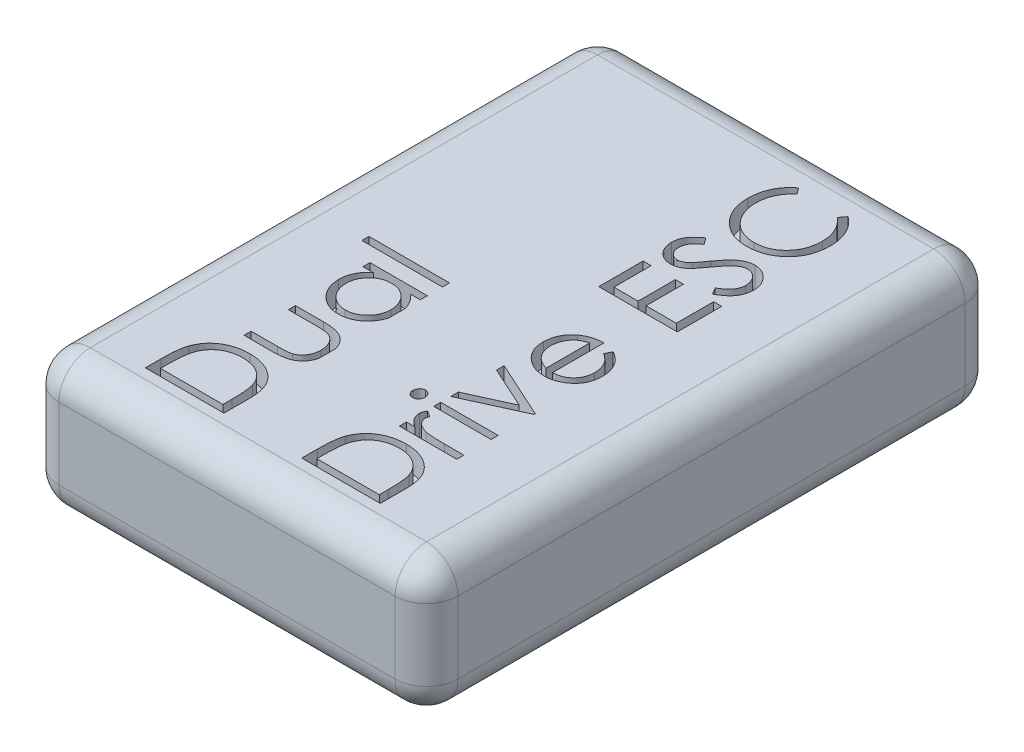
SolidWorks part; units mm, degrees
ref_plane "Front Plane" through (0, 0, 0) normal (0, 0, 1) x (1, 0, 0)
ref_plane "Top Plane" through (0, 0, 0) normal (0, 1, 0) x (1, 0, 0)
ref_plane "Right Plane" through (0, 0, 0) normal (1, 0, 0) x (0, 0, -1)
sketch "Sketch1" plane through (0, 0, 0) normal (0, 1, 0) x (1, 0, 0)
  line L1 (0, 0) -> (17.78, 0)
  line L2 (0, 0) -> (0, 25.4)
  line L3 (0, 25.4) -> (17.78, 25.4)
  line L4 (17.78, 0) -> (17.78, 25.4)
  dimension "D1" = 17.78
  dimension "D2" = 25.4
extrude "Boss-Extrude1" add sketch "Sketch1" along normal blind 6
fillet "Fillet1" radius 1.4 12 edges at (0, 0, -12.7) (8.89, 0, 0) (17.78, 0, -12.7) (8.89, 0, -25.4) (0, 6, -12.7) (17.78, 6, -12.7) (8.89, 6, -25.4) (0, 3, -25.4) (17.78, 3, -25.4) (17.78, 3, 0) (0, 3, 0) (8.89, 6, 0)
sketch "Sketch2" plane through (0, 6, 0) normal (0, 1, 0) x (1, 0, 0)
  line L0 (6.9039, 1.4) -> (6.9039, 24)
  line L1 (1.4, 1.4) -> (16.38, 1.4) construction
  line L2 (16.38, 24) -> (1.4, 24) construction
  line L3 (6.9039, 1.8487) -> (3.4039, 1.8487)
  line L4 (3.4039, 1.8487) -> (3.4039, 2.5554)
  line L5 (6.9039, 2.9334) -> (6.9039, 1.8487)
  line L6 (6.5449, 2.1628) -> (6.5449, 2.5646)
  line L7 (3.7629, 2.4089) -> (3.7629, 2.1628)
  line L8 (3.7629, 2.1628) -> (6.5449, 2.1628)
  line L9 (4.3462, 5.3038) -> (4.3462, 5.6179)
  line L10 (4.3462, 5.6179) -> (5.5325, 5.6179)
  line L11 (5.5325, 7.2782) -> (4.3462, 7.2782)
  line L12 (4.3462, 7.2782) -> (4.3462, 7.5923)
  line L13 (4.3462, 7.5923) -> (5.5914, 7.5923)
  line L14 (5.5683, 5.3038) -> (4.3462, 5.3038)
  line L15 (4.3462, 10.9128) -> (6.9039, 10.9128)
  line L16 (6.9039, 10.9128) -> (6.9039, 10.5987)
  line L17 (6.9039, 10.5987) -> (6.4615, 10.5987)
  line L18 (4.8195, 10.5987) -> (4.3462, 10.5987)
  line L19 (4.3462, 10.5987) -> (4.3462, 10.9128)
  line L20 (3.3141, 11.5859) -> (3.3141, 11.9)
  line L21 (3.3141, 11.9) -> (6.9039, 11.9)
  line L22 (6.9039, 11.9) -> (6.9039, 11.5859)
  line L23 (6.9039, 11.5859) -> (3.3141, 11.5859)
  line L24 (13.8718, 1.8487) -> (10.3718, 1.8487)
  line L25 (10.3718, 1.8487) -> (10.3718, 2.5554)
  line L26 (13.8718, 2.9334) -> (13.8718, 1.8487)
  line L27 (13.5129, 2.1628) -> (13.5129, 2.5646)
  line L28 (10.7308, 2.4089) -> (10.7308, 2.1628)
  line L29 (10.7308, 2.1628) -> (13.5129, 2.1628)
  line L30 (11.3141, 5.259) -> (11.3141, 5.5731)
  line L31 (11.3141, 5.5731) -> (11.6907, 5.5731)
  line L32 (11.3569, 6.4705) -> (11.629, 6.298)
  line L33 (13.0123, 5.5731) -> (13.8718, 5.5731)
  line L34 (13.8718, 5.5731) -> (13.8718, 5.259)
  line L35 (13.8718, 5.259) -> (11.3141, 5.259)
  line L36 (11.3141, 6.7846) -> (11.3141, 7.0987)
  line L37 (11.3141, 7.0987) -> (13.8718, 7.0987)
  line L38 (13.8718, 7.0987) -> (13.8718, 6.7846)
  line L39 (13.8718, 6.7846) -> (11.3141, 6.7846)
  line L40 (11.3141, 7.5474) -> (11.3141, 7.8875)
  line L41 (11.3141, 7.8875) -> (13.1763, 8.7365)
  line L42 (13.1763, 8.7365) -> (11.3141, 9.5856)
  line L43 (11.3141, 9.5856) -> (11.3141, 9.9256)
  line L44 (11.3141, 9.9256) -> (13.8718, 8.759)
  line L45 (13.8718, 8.759) -> (13.8718, 8.7141)
  line L46 (13.8718, 8.7141) -> (11.3141, 7.5474)
  line L47 (13.0641, 12.6081) -> (13.2107, 12.8872)
  line L48 (12.6603, 13.0218) -> (12.6603, 10.7333)
  line L49 (12.3462, 10.7663) -> (12.3462, 12.7077)
  line L50 (10.3718, 15.0859) -> (10.3718, 17.0603)
  line L51 (10.3718, 17.0603) -> (10.7308, 17.0603)
  line L52 (10.7308, 17.0603) -> (10.7308, 15.4)
  line L53 (10.7308, 15.4) -> (11.8077, 15.4)
  line L54 (11.8077, 15.4) -> (11.8077, 17.0603)
  line L55 (11.8077, 17.0603) -> (12.1667, 17.0603)
  line L56 (12.1667, 17.0603) -> (12.1667, 15.4)
  line L57 (12.1667, 15.4) -> (13.5129, 15.4)
  line L58 (13.5129, 15.4) -> (13.5129, 17.0603)
  line L59 (13.5129, 17.0603) -> (13.8718, 17.0603)
  line L60 (13.8718, 17.0603) -> (13.8718, 15.0859)
  line L61 (13.8718, 15.0859) -> (10.3718, 15.0859)
  line L62 (13.1967, 17.3295) -> (13.0193, 17.6254)
  line L63 (10.8745, 19.3487) -> (11.0898, 19.0648)
  line L64 (11.0141, 23.3423) -> (11.2244, 23.0675)
  line L65 (13.0193, 23.0675) -> (13.2275, 23.3423)
  spline S0 degree 3 poles (3.4039, 2.5554) (3.4044, 2.6742) (3.4069, 2.8459) (3.4202, 3.0661) (3.4342, 3.2115) (3.4514, 3.344) (3.4785, 3.4953) (3.5071, 3.601) (3.5301, 3.666) knots 0 0 0 0 0.317406 0.458844 0.589367 0.707831 0.81577 1 1 1 1
  spline S1 degree 3 poles (3.5301, 3.666) (3.5587, 3.7468) (3.6111, 3.8635) (3.6987, 4.0082) (3.7726, 4.1087) (3.8544, 4.2022) (3.9436, 4.2899) (4.0422, 4.3696) (4.1483, 4.4425) (4.2606, 4.5082) (4.3789, 4.5654) (4.5027, 4.6128) (4.6315, 4.6522) (4.7657, 4.6832) (4.9547, 4.7121) (5.0999, 4.721) (5.1981, 4.7205) knots 0 0 0 0 0.121697 0.181159 0.240077 0.298686 0.357633 0.417592 0.478482 0.540397 0.602336 0.664997 0.728553 0.793646 0.860531 1 1 1 1
  spline S2 degree 3 poles (5.1981, 4.7205) (5.2833, 4.7209) (5.4093, 4.7133) (5.5741, 4.6913) (5.6917, 4.6663) (5.8061, 4.6359) (5.9159, 4.5969) (6.0222, 4.5523) (6.1237, 4.5003) (6.2197, 4.4431) (6.3103, 4.3821) (6.3934, 4.3159) (6.4713, 4.2464) (6.5419, 4.1721) (6.6063, 4.0938) (6.6637, 4.0112) (6.7147, 3.9238) (6.7604, 3.8304) (6.7985, 3.7281) (6.8315, 3.6173) (6.8578, 3.4975) (6.8789, 3.369) (6.8985, 3.1802) (6.9044, 3.0337) (6.9039, 2.9334) knots 0 0 0 0 0.090813 0.134304 0.177036 0.218837 0.260262 0.3011 0.341637 0.381609 0.420148 0.45791 0.494761 0.531219 0.566961 0.602742 0.638232 0.674761 0.713378 0.754425 0.797802 0.843979 0.893064 1 1 1 1
  spline S3 degree 3 poles (6.5449, 2.5646) (6.5449, 2.6756) (6.5427, 2.8353) (6.5332, 3.0389) (6.5236, 3.171) (6.5109, 3.2893) (6.4934, 3.4202) (6.4731, 3.5105) (6.4559, 3.5651) knots 0 0 0 0 0.330628 0.475549 0.606746 0.725024 0.829742 1 1 1 1
  spline S4 degree 3 poles (6.4559, 3.5651) (6.4344, 3.6283) (6.3986, 3.7215) (6.3338, 3.8358) (6.2804, 3.9159) (6.2197, 3.9902) (6.1532, 4.0596) (6.0804, 4.1241) (6.0014, 4.1825) (5.9172, 4.2354) (5.8276, 4.2808) (5.7339, 4.3204) (5.6352, 4.3517) (5.5323, 4.3764) (5.3864, 4.4) (5.2737, 4.4064) (5.1974, 4.4064) knots 0 0 0 0 0.123333 0.183117 0.241773 0.300566 0.359665 0.418864 0.479511 0.540462 0.601913 0.664467 0.727807 0.792475 0.859249 1 1 1 1
  spline S5 degree 3 poles (5.1974, 4.4064) (5.1169, 4.4073) (4.9984, 4.399) (4.8445, 4.3737) (4.7356, 4.3469) (4.6309, 4.3128) (4.5311, 4.2702) (4.4351, 4.2215) (4.3451, 4.1636) (4.26, 4.1002) (4.182, 4.0298) (4.111, 3.9536) (4.0459, 3.8724) (3.9892, 3.7838) (3.9207, 3.6572) (3.8828, 3.5545) (3.861, 3.4844) knots 0 0 0 0 0.137813 0.203226 0.267174 0.330024 0.391794 0.453084 0.514334 0.575 0.634865 0.694116 0.753442 0.813126 0.87408 1 1 1 1
  spline S6 degree 3 poles (3.861, 3.4844) (3.8423, 3.4224) (3.821, 3.321) (3.8003, 3.1762) (3.7861, 3.0483) (3.7761, 2.9073) (3.7655, 2.6928) (3.7625, 2.5251) (3.7629, 2.4089) knots 0 0 0 0 0.179285 0.286583 0.405111 0.535593 0.67819 1 1 1 1
  spline S7 degree 3 poles (5.5325, 5.6179) (5.5991, 5.6183) (5.695, 5.6185) (5.8172, 5.6245) (5.8962, 5.6299) (5.9669, 5.6369) (6.0444, 5.6472) (6.0983, 5.6577) (6.1306, 5.6677) knots 0 0 0 0 0.33212 0.477936 0.609932 0.727032 0.831671 1 1 1 1
  spline S8 degree 3 poles (6.1306, 5.6677) (6.1682, 5.6808) (6.2243, 5.7018) (6.292, 5.7422) (6.3403, 5.775) (6.3851, 5.8129) (6.4263, 5.8554) (6.4655, 5.901) (6.5119, 5.9687) (6.5616, 6.0614) (6.6204, 6.2274) (6.6345, 6.3621) (6.6347, 6.453) knots 0 0 0 0 0.119716 0.178086 0.235971 0.29461 0.353536 0.413161 0.474545 0.599234 0.727029 1 1 1 1
  spline S9 degree 3 poles (6.6347, 6.453) (6.6342, 6.5434) (6.6209, 6.6765) (6.5639, 6.8402) (6.5061, 6.9471) (6.4353, 7.0409) (6.3251, 7.1454) (6.2264, 7.2019) (6.1558, 7.2263) knots 0 0 0 0 0.279837 0.408371 0.533043 0.653596 0.770016 1 1 1 1
  spline S10 degree 3 poles (6.1558, 7.2263) (6.1252, 7.2365) (6.073, 7.2478) (5.9961, 7.2587) (5.9232, 7.2664) (5.8399, 7.2718) (5.7085, 7.2761) (5.605, 7.279) (5.5325, 7.2782) knots 0 0 0 0 0.154074 0.254591 0.371465 0.504755 0.653494 1 1 1 1
  spline S11 degree 3 poles (5.5914, 7.5923) (5.6735, 7.5919) (5.7929, 7.5892) (5.9465, 7.576) (6.0496, 7.5619) (6.1445, 7.5447) (6.2312, 7.5231) (6.3099, 7.4971) (6.3816, 7.4678) (6.4467, 7.4332) (6.5084, 7.3964) (6.5652, 7.3538) (6.6202, 7.3093) (6.6695, 7.2587) (6.717, 7.2059) (6.7597, 7.1478) (6.799, 7.0863) (6.8342, 7.0207) (6.8652, 6.9512) (6.891, 6.8775) (6.912, 6.7997) (6.9288, 6.718) (6.9449, 6.6012) (6.949, 6.5113) (6.9488, 6.4502) knots 0 0 0 0 0.120709 0.175567 0.226556 0.273743 0.317339 0.357879 0.395473 0.431138 0.466151 0.501072 0.535484 0.569994 0.604816 0.639941 0.675791 0.712081 0.749315 0.787578 0.826765 0.867814 0.91015 1 1 1 1
  spline S12 degree 3 poles (6.9488, 6.4502) (6.949, 6.3891) (6.9449, 6.2991) (6.9288, 6.1823) (6.9119, 6.1005) (6.8911, 6.0223) (6.865, 5.9483) (6.8342, 5.8783) (6.7991, 5.8121) (6.7596, 5.7501) (6.7162, 5.6922) (6.6699, 5.6376) (6.6191, 5.5877) (6.5644, 5.5421) (6.5058, 5.5007) (6.4441, 5.4628) (6.378, 5.4284) (6.3055, 5.3989) (6.2252, 5.3729) (6.1363, 5.3516) (6.0388, 5.3342) (5.9333, 5.3203) (5.7756, 5.3068) (5.6529, 5.3043) (5.5683, 5.3038) knots 0 0 0 0 0.088737 0.130549 0.17109 0.210119 0.247908 0.284992 0.321132 0.356538 0.391704 0.426128 0.460451 0.494916 0.529482 0.564528 0.600052 0.637495 0.678178 0.722552 0.770157 0.82186 0.877053 1 1 1 1
  spline S13 degree 3 poles (6.4615, 10.5987) (6.5404, 10.5308) (6.6526, 10.4237) (6.766, 10.2561) (6.8343, 10.1277) (6.8854, 9.9927) (6.9348, 9.8027) (6.9496, 9.6543) (6.9488, 9.554) knots 0 0 0 0 0.26246 0.386305 0.507193 0.627322 0.748159 1 1 1 1
  spline S14 degree 3 poles (6.9488, 9.554) (6.9485, 9.465) (6.9371, 9.3327) (6.8962, 9.1627) (6.8543, 9.0414) (6.7987, 8.9257) (6.7322, 8.8147) (6.653, 8.7088) (6.5624, 8.6097) (6.464, 8.5185) (6.359, 8.4384) (6.248, 8.3717) (6.1323, 8.3159) (6.0109, 8.2729) (5.8402, 8.2322) (5.7075, 8.2207) (5.618, 8.2205) knots 0 0 0 0 0.127433 0.189004 0.24993 0.310668 0.372329 0.434939 0.499576 0.564191 0.626735 0.688109 0.749294 0.810331 0.871901 1 1 1 1
  spline S15 degree 3 poles (5.618, 8.2205) (5.5302, 8.221) (5.3996, 8.2318) (5.2319, 8.2738) (5.1125, 8.3173) (4.9982, 8.3731) (4.8888, 8.441) (4.784, 8.5211) (4.6863, 8.6133) (4.5961, 8.7133) (4.5177, 8.8202) (4.45, 8.9314) (4.3963, 9.0486) (4.3529, 9.1702) (4.3123, 9.3414) (4.3021, 9.4744) (4.3013, 9.5639) knots 0 0 0 0 0.126079 0.186904 0.247574 0.308003 0.369132 0.432033 0.496791 0.561611 0.624914 0.686726 0.748079 0.809582 0.871631 1 1 1 1
  spline S16 degree 3 poles (4.3013, 9.5639) (4.3017, 9.666) (4.3147, 9.8178) (4.3688, 10.0098) (4.4224, 10.1447) (4.4952, 10.2711) (4.6168, 10.4342) (4.7356, 10.5358) (4.8195, 10.5987) knots 0 0 0 0 0.254681 0.376055 0.495308 0.61515 0.738121 1 1 1 1
  spline S17 degree 3 poles (4.6154, 9.5681) (4.6158, 9.4776) (4.6308, 9.3422) (4.6875, 9.1712) (4.7444, 9.0499) (4.8176, 8.9381) (4.9037, 8.8363) (5.0043, 8.7478) (5.1158, 8.6717) (5.2359, 8.6107) (5.403, 8.5528) (5.5341, 8.5335) (5.6215, 8.5346) knots 0 0 0 0 0.169607 0.252496 0.336272 0.419777 0.50203 0.585103 0.669819 0.754165 0.836645 1 1 1 1
  spline S18 degree 3 poles (5.6215, 8.5346) (5.7084, 8.5355) (5.8398, 8.5517) (6.0062, 8.6121) (6.1274, 8.673) (6.2399, 8.75) (6.3424, 8.8384) (6.4298, 8.9406) (6.5031, 9.0535) (6.5622, 9.1741) (6.6176, 9.3436) (6.6351, 9.4764) (6.6347, 9.5653) knots 0 0 0 0 0.162873 0.245092 0.330422 0.416116 0.499851 0.583013 0.66713 0.751291 0.833771 1 1 1 1
  spline S19 degree 3 poles (6.6347, 9.5653) (6.634, 9.6555) (6.6192, 9.7915) (6.5617, 9.9639) (6.5041, 10.0878) (6.4323, 10.2032) (6.3483, 10.3063) (6.2512, 10.3946) (6.1433, 10.4681) (6.0257, 10.5264) (5.8566, 10.5842) (5.7213, 10.5981) (5.6307, 10.5987) knots 0 0 0 0 0.168704 0.252748 0.338456 0.42334 0.505813 0.586129 0.667469 0.748852 0.830411 1 1 1 1
  spline S20 degree 3 poles (5.6307, 10.5987) (5.5611, 10.5985) (5.4581, 10.5897) (5.3259, 10.5585) (5.2325, 10.5261) (5.1438, 10.4836) (5.0594, 10.4324) (4.9795, 10.3715) (4.9054, 10.3019) (4.8377, 10.2257) (4.7774, 10.1452) (4.7278, 10.0592) (4.6867, 9.9693) (4.6541, 9.8752) (4.6244, 9.7416) (4.6144, 9.6382) (4.6154, 9.5681) knots 0 0 0 0 0.129188 0.191219 0.251913 0.312507 0.373494 0.435152 0.498741 0.562095 0.624187 0.685476 0.746097 0.807612 0.869967 1 1 1 1
  spline S21 degree 3 poles (10.3718, 2.5554) (10.3723, 2.6742) (10.3748, 2.8459) (10.3882, 3.0661) (10.4021, 3.2115) (10.4193, 3.344) (10.4464, 3.4953) (10.475, 3.601) (10.498, 3.666) knots 0 0 0 0 0.317406 0.458844 0.589367 0.707831 0.81577 1 1 1 1
  spline S22 degree 3 poles (10.498, 3.666) (10.5266, 3.7468) (10.579, 3.8635) (10.6667, 4.0082) (10.7405, 4.1087) (10.8224, 4.2022) (10.9116, 4.2899) (11.0101, 4.3696) (11.1162, 4.4425) (11.2285, 4.5082) (11.3468, 4.5654) (11.4706, 4.6128) (11.5994, 4.6522) (11.7336, 4.6832) (11.9226, 4.7121) (12.0678, 4.721) (12.166, 4.7205) knots 0 0 0 0 0.121697 0.181159 0.240077 0.298686 0.357633 0.417592 0.478482 0.540397 0.602336 0.664997 0.728553 0.793646 0.860531 1 1 1 1
  spline S23 degree 3 poles (12.166, 4.7205) (12.2513, 4.7209) (12.3773, 4.7133) (12.5421, 4.6913) (12.6597, 4.6663) (12.774, 4.6359) (12.8838, 4.5969) (12.9902, 4.5523) (13.0916, 4.5003) (13.1877, 4.4431) (13.2782, 4.3821) (13.3614, 4.3159) (13.4393, 4.2464) (13.5098, 4.1721) (13.5743, 4.0938) (13.6316, 4.0112) (13.6827, 3.9238) (13.7284, 3.8304) (13.7665, 3.7281) (13.7995, 3.6173) (13.8257, 3.4975) (13.8469, 3.369) (13.8664, 3.1802) (13.8724, 3.0337) (13.8718, 2.9334) knots 0 0 0 0 0.090813 0.134304 0.177036 0.218837 0.260262 0.3011 0.341637 0.381609 0.420148 0.45791 0.494761 0.531219 0.566961 0.602742 0.638232 0.674761 0.713378 0.754425 0.797802 0.843979 0.893064 1 1 1 1
  spline S24 degree 3 poles (13.5129, 2.5646) (13.5128, 2.6756) (13.5107, 2.8353) (13.5011, 3.0389) (13.4915, 3.171) (13.4788, 3.2893) (13.4613, 3.4202) (13.441, 3.5105) (13.4238, 3.5651) knots 0 0 0 0 0.330628 0.475549 0.606746 0.725024 0.829742 1 1 1 1
  spline S25 degree 3 poles (13.4238, 3.5651) (13.4024, 3.6283) (13.3666, 3.7215) (13.3017, 3.8358) (13.2483, 3.9159) (13.1877, 3.9902) (13.1211, 4.0596) (13.0483, 4.1241) (12.9694, 4.1825) (12.8852, 4.2354) (12.7956, 4.2808) (12.7018, 4.3204) (12.6031, 4.3517) (12.5003, 4.3764) (12.3544, 4.4) (12.2417, 4.4064) (12.1653, 4.4064) knots 0 0 0 0 0.123333 0.183117 0.241773 0.300566 0.359665 0.418864 0.479511 0.540462 0.601913 0.664467 0.727807 0.792475 0.859249 1 1 1 1
  spline S26 degree 3 poles (12.1653, 4.4064) (12.0849, 4.4073) (11.9664, 4.399) (11.8125, 4.3737) (11.7035, 4.3469) (11.5988, 4.3128) (11.499, 4.2702) (11.403, 4.2215) (11.313, 4.1636) (11.2279, 4.1002) (11.15, 4.0298) (11.079, 3.9536) (11.0138, 3.8724) (10.9572, 3.7838) (10.8886, 3.6572) (10.8508, 3.5545) (10.829, 3.4844) knots 0 0 0 0 0.137813 0.203226 0.267174 0.330024 0.391794 0.453084 0.514334 0.575 0.634865 0.694116 0.753442 0.813126 0.87408 1 1 1 1
  spline S27 degree 3 poles (10.829, 3.4844) (10.8102, 3.4224) (10.789, 3.321) (10.7682, 3.1762) (10.7541, 3.0483) (10.744, 2.9073) (10.7334, 2.6928) (10.7304, 2.5251) (10.7308, 2.4089) knots 0 0 0 0 0.179285 0.286583 0.405111 0.535593 0.67819 1 1 1 1
  spline S28 degree 3 poles (11.6907, 5.5731) (11.6227, 5.6159) (11.5294, 5.6845) (11.4257, 5.7896) (11.3673, 5.8675) (11.3233, 5.9477) (11.282, 6.0557) (11.2694, 6.1409) (11.2693, 6.1971) knots 0 0 0 0 0.306021 0.438854 0.560992 0.675734 0.786178 1 1 1 1
  spline S29 degree 3 poles (11.2693, 6.1971) (11.2696, 6.2421) (11.2865, 6.3385) (11.3301, 6.4262) (11.3569, 6.4705) knots 0 0 0 0 0.463523 1 1 1 1
  spline S30 degree 3 poles (11.629, 6.298) (11.6163, 6.2694) (11.593, 6.218) (11.5837, 6.1622) (11.5834, 6.1375) knots 0 0 0 0 0.56023 1 1 1 1
  spline S31 degree 3 poles (11.5834, 6.1375) (11.5831, 6.0858) (11.6026, 6.0074) (11.6582, 5.9119) (11.7065, 5.854) (11.7531, 5.8089) (11.7938, 5.7766) (11.8399, 5.7475) (11.8896, 5.7193) (11.9441, 5.6931) (12.0254, 5.661) (12.0899, 5.6409) (12.1345, 5.6292) knots 0 0 0 0 0.191278 0.294662 0.409747 0.471345 0.53582 0.603222 0.674199 0.748603 0.828338 1 1 1 1
  spline S32 degree 3 poles (12.1345, 5.6292) (12.1793, 5.6173) (12.2545, 5.6061) (12.3643, 5.5937) (12.467, 5.5866) (12.5838, 5.58) (12.7671, 5.5748) (12.9115, 5.5725) (13.0123, 5.5731) knots 0 0 0 0 0.157726 0.258598 0.375889 0.508164 0.657032 1 1 1 1
  spline S33 degree 3 poles (10.2372, 6.9403) (10.2373, 6.9783) (10.246, 7.0357) (10.2808, 7.1034) (10.3152, 7.148) (10.3558, 7.1862) (10.4189, 7.2222) (10.4722, 7.2335) (10.5079, 7.2333) knots 0 0 0 0 0.258284 0.384341 0.51198 0.638632 0.75923 1 1 1 1
  spline S34 degree 3 poles (10.5079, 7.2333) (10.5428, 7.2334) (10.5953, 7.2221) (10.6572, 7.1859) (10.6977, 7.148) (10.7321, 7.1034) (10.7669, 7.0357) (10.7756, 6.9783) (10.7757, 6.9403) knots 0 0 0 0 0.237546 0.357497 0.484917 0.613329 0.74015 1 1 1 1
  spline S35 degree 3 poles (10.7757, 6.9403) (10.7759, 6.9029) (10.7665, 6.8464) (10.7321, 6.7793) (10.6979, 6.7346) (10.657, 6.6974) (10.5953, 6.6612) (10.5428, 6.65) (10.5079, 6.65) knots 0 0 0 0 0.256661 0.384213 0.513365 0.640443 0.761085 1 1 1 1
  spline S36 degree 3 poles (10.5079, 6.65) (10.4722, 6.6498) (10.4188, 6.6611) (10.356, 6.6972) (10.315, 6.7346) (10.2808, 6.7793) (10.2464, 6.8464) (10.237, 6.9029) (10.2372, 6.9403) knots 0 0 0 0 0.242149 0.363437 0.489745 0.618115 0.744894 1 1 1 1
  spline S37 degree 3 poles (13.2107, 12.8872) (13.2882, 12.8455) (13.3975, 12.7766) (13.5265, 12.6691) (13.6081, 12.584) (13.6802, 12.4948) (13.7424, 12.3997) (13.7958, 12.2997) (13.8395, 12.1935) (13.8739, 12.0813) (13.9087, 11.9191) (13.9164, 11.792) (13.9167, 11.7058) knots 0 0 0 0 0.181689 0.265546 0.346039 0.424597 0.501912 0.580013 0.658291 0.738533 0.821867 1 1 1 1
  spline S38 degree 3 poles (13.9167, 11.7058) (13.9167, 11.61) (13.9057, 11.4691) (13.8625, 11.2899) (13.8186, 11.1667) (13.7612, 11.0519) (13.6912, 10.9454) (13.6091, 10.8466) (13.5141, 10.7586) (13.4124, 10.6793) (13.3064, 10.6094) (13.1966, 10.5512) (13.0835, 10.5031) (12.9675, 10.4652) (12.8069, 10.4289) (12.683, 10.4202) (12.6, 10.4192) knots 0 0 0 0 0.139628 0.204795 0.268132 0.32981 0.391297 0.453429 0.516546 0.579625 0.641112 0.701287 0.760489 0.819934 0.878921 1 1 1 1
  spline S39 degree 3 poles (12.6, 10.4192) (12.5222, 10.4202) (12.4061, 10.4275) (12.2555, 10.4591) (12.1467, 10.4912) (12.0411, 10.5328) (11.9036, 10.601) (11.8075, 10.6662) (11.746, 10.7137) knots 0 0 0 0 0.253768 0.377428 0.500551 0.623296 0.746578 1 1 1 1
  spline S40 degree 3 poles (11.746, 10.7137) (11.6698, 10.7736) (11.5656, 10.8737) (11.4535, 11.0274) (11.3858, 11.1493) (11.3337, 11.2795) (11.2831, 11.4665) (11.2694, 11.6138) (11.2693, 11.7135) knots 0 0 0 0 0.253207 0.374634 0.495346 0.616346 0.739634 1 1 1 1
  spline S41 degree 3 poles (11.2693, 11.7135) (11.2687, 11.8164) (11.2839, 11.9682) (11.3368, 12.161) (11.3931, 12.2943) (11.4631, 12.4206) (11.5826, 12.5785) (11.6919, 12.6821) (11.7727, 12.7434) knots 0 0 0 0 0.259049 0.381904 0.502516 0.622728 0.744726 1 1 1 1
  spline S42 degree 3 poles (11.7727, 12.7434) (11.8316, 12.7893) (11.9272, 12.8492) (12.064, 12.9129) (12.1729, 12.9512) (12.2867, 12.9822) (12.4491, 13.0128) (12.575, 13.0202) (12.6603, 13.0218) knots 0 0 0 0 0.236255 0.356174 0.47725 0.60154 0.729618 1 1 1 1
  spline S43 degree 3 poles (12.6603, 10.7333) (12.7265, 10.7351) (12.8244, 10.744) (12.9496, 10.7743) (13.0367, 10.8055) (13.1196, 10.8434) (13.1978, 10.8898) (13.2708, 10.9451) (13.3394, 11.0069) (13.4005, 11.0756) (13.4551, 11.1478) (13.5009, 11.2247) (13.5381, 11.3056) (13.5672, 11.3904) (13.5942, 11.5104) (13.603, 11.6035) (13.6026, 11.6665) knots 0 0 0 0 0.134476 0.198391 0.260753 0.321829 0.383037 0.444653 0.507398 0.569825 0.630778 0.690929 0.750945 0.811049 0.872331 1 1 1 1
  spline S44 degree 3 poles (13.6026, 11.6665) (13.603, 11.7287) (13.5954, 11.822) (13.5703, 11.944) (13.5434, 12.033) (13.5118, 12.1185) (13.4747, 12.1981) (13.4323, 12.2708) (13.3842, 12.339) (13.3251, 12.4047) (13.2212, 12.4993) (13.1303, 12.5649) (13.0641, 12.6081) knots 0 0 0 0 0.163889 0.245674 0.327919 0.408809 0.485689 0.559113 0.630217 0.705259 0.79157 1 1 1 1
  spline S45 degree 3 poles (12.3462, 12.7077) (12.2655, 12.6883) (12.1521, 12.6476) (12.0147, 12.576) (11.9291, 12.5141) (11.853, 12.4446) (11.7875, 12.3632) (11.7271, 12.2735) (11.6768, 12.1736) (11.6356, 12.0675) (11.5948, 11.9204) (11.5842, 11.8058) (11.5834, 11.7296) knots 0 0 0 0 0.184782 0.267525 0.344439 0.419646 0.496623 0.576672 0.660317 0.74526 0.830065 1 1 1 1
  spline S46 degree 3 poles (11.5834, 11.7296) (11.5831, 11.6677) (11.5901, 11.5757) (11.6154, 11.4572) (11.6427, 11.3729) (11.676, 11.2918) (11.7308, 11.1871) (11.7848, 11.1161) (11.8232, 11.0706) knots 0 0 0 0 0.259163 0.384194 0.506328 0.629067 0.750648 1 1 1 1
  spline S47 degree 3 poles (11.8232, 11.0706) (11.8525, 11.0357) (11.9035, 10.9886) (11.9783, 10.9315) (12.0417, 10.8928) (12.11, 10.8561) (12.2105, 10.8102) (12.2908, 10.7827) (12.3462, 10.7663) knots 0 0 0 0 0.222589 0.338513 0.459696 0.585519 0.717507 1 1 1 1
  spline S48 degree 3 poles (13.0193, 17.6254) (13.1082, 17.6766) (13.233, 17.7575) (13.3742, 17.8847) (13.4571, 17.9797) (13.5223, 18.0779) (13.5837, 18.2129) (13.6028, 18.3218) (13.6026, 18.3938) knots 0 0 0 0 0.304646 0.438547 0.562322 0.677433 0.786897 1 1 1 1
  spline S49 degree 3 poles (13.6026, 18.3938) (13.6029, 18.4546) (13.5931, 18.5456) (13.5578, 18.6617) (13.5224, 18.7445) (13.4788, 18.8213) (13.4273, 18.8896) (13.3679, 18.9474) (13.3027, 18.9952) (13.2328, 19.0323) (13.1369, 19.0697) (13.0599, 19.0786) (13.0095, 19.0795) knots 0 0 0 0 0.180992 0.270379 0.360478 0.448694 0.532623 0.614316 0.694491 0.772638 0.849284 1 1 1 1
  spline S50 degree 3 poles (13.0095, 19.0795) (12.9503, 19.0801) (12.8269, 19.0553) (12.7181, 18.9926) (12.6659, 18.954) knots 0 0 0 0 0.475391 1 1 1 1
  spline S51 degree 3 poles (12.6659, 18.954) (12.6233, 18.9218) (12.5589, 18.8671) (12.4765, 18.7827) (12.4082, 18.7081) (12.3371, 18.6248) (12.2338, 18.4975) (12.1591, 18.3943) (12.1078, 18.323) knots 0 0 0 0 0.189534 0.299205 0.418374 0.548366 0.688129 1 1 1 1
  spline S52 degree 3 poles (12.1078, 18.323) (12.0583, 18.2522) (11.9847, 18.153) (11.889, 18.0293) (11.8267, 17.952) (11.7701, 17.8856) (11.7083, 17.8166) (11.6616, 17.7736) (11.6318, 17.7495) knots 0 0 0 0 0.347082 0.495568 0.628357 0.74552 0.845831 1 1 1 1
  spline S53 degree 3 poles (11.6318, 17.7495) (11.5917, 17.7186) (11.5302, 17.6753) (11.4426, 17.6295) (11.3764, 17.6022) (11.3089, 17.5801) (11.2168, 17.5595) (11.1461, 17.5536) (11.0989, 17.5538) knots 0 0 0 0 0.26255 0.388252 0.511531 0.633734 0.755402 1 1 1 1
  spline S54 degree 3 poles (11.0989, 17.5538) (11.0257, 17.5537) (10.9167, 17.5675) (10.7794, 17.6141) (10.6831, 17.6623) (10.595, 17.7246) (10.5145, 17.7969) (10.4459, 17.8822) (10.3869, 17.9767) (10.3403, 18.0795) (10.2946, 18.225) (10.2828, 18.3397) (10.2821, 18.4162) knots 0 0 0 0 0.165751 0.246237 0.327404 0.408726 0.48963 0.57161 0.655742 0.741224 0.826577 1 1 1 1
  spline S55 degree 3 poles (10.2821, 18.4162) (10.2817, 18.4982) (10.2976, 18.6209) (10.3508, 18.7765) (10.3972, 18.8697) (10.4433, 18.9429) (10.4853, 18.9986) (10.5336, 19.0554) (10.5892, 19.1126) (10.651, 19.1709) (10.745, 19.2519) (10.8208, 19.3106) (10.8745, 19.3487) knots 0 0 0 0 0.213204 0.318562 0.426501 0.48334 0.543285 0.607974 0.677199 0.750741 0.828752 1 1 1 1
  spline S56 degree 3 poles (11.0898, 19.0648) (11.0468, 19.0322) (10.9867, 18.9828) (10.9111, 18.9173) (10.8639, 18.8704) (10.8205, 18.8275) (10.784, 18.7851) (10.7532, 18.7449) (10.7203, 18.6943) (10.6887, 18.6303) (10.6512, 18.5233) (10.6415, 18.438) (10.6411, 18.3812) knots 0 0 0 0 0.18959 0.274128 0.352111 0.423687 0.489026 0.548936 0.601892 0.701259 0.799633 1 1 1 1
  spline S57 degree 3 poles (10.6411, 18.3812) (10.6398, 18.3115) (10.6555, 18.2097) (10.7095, 18.0871) (10.766, 18.0104) (10.8333, 17.9472) (10.9361, 17.8848) (11.0253, 17.8681) (11.0842, 17.8679) knots 0 0 0 0 0.275822 0.401869 0.527875 0.650459 0.765964 1 1 1 1
  spline S58 degree 3 poles (11.0842, 17.8679) (11.122, 17.867) (11.1781, 17.875) (11.2514, 17.8944) (11.3062, 17.9165) (11.3616, 17.9474) (11.4423, 18.0046) (11.4985, 18.0592) (11.5364, 18.0986) knots 0 0 0 0 0.216059 0.322956 0.434131 0.553424 0.686081 1 1 1 1
  spline S59 degree 3 poles (11.5364, 18.0986) (11.5529, 18.1166) (11.58, 18.1495) (11.6189, 18.2017) (11.6595, 18.2552) (11.7065, 18.3191) (11.782, 18.4251) (11.8427, 18.5092) (11.8849, 18.5691) knots 0 0 0 0 0.124952 0.218094 0.333502 0.468789 0.624938 1 1 1 1
  spline S60 degree 3 poles (11.8849, 18.5691) (11.9382, 18.6427) (12.0164, 18.7491) (12.1251, 18.8802) (12.2015, 18.9656) (12.275, 19.0425) (12.3465, 19.11) (12.4156, 19.1684) (12.5035, 19.2321) (12.6125, 19.2964) (12.7871, 19.3691) (12.9243, 19.3936) (13.0144, 19.3936) knots 0 0 0 0 0.187763 0.272381 0.351302 0.424312 0.491882 0.554203 0.610843 0.715918 0.81455 1 1 1 1
  spline S61 degree 3 poles (13.0144, 19.3936) (13.0766, 19.3946) (13.1687, 19.3844) (13.2878, 19.3547) (13.3725, 19.3219) (13.4549, 19.2812) (13.5332, 19.2303) (13.6089, 19.1709) (13.6801, 19.1029) (13.7455, 19.0285) (13.8035, 18.9495) (13.8529, 18.8669) (13.8923, 18.7797) (13.9232, 18.6888) (13.9537, 18.5607) (13.9618, 18.4609) (13.9616, 18.3938) knots 0 0 0 0 0.121796 0.180952 0.240299 0.299757 0.3608 0.423165 0.488346 0.553642 0.617281 0.680182 0.742142 0.804628 0.868236 1 1 1 1
  spline S62 degree 3 poles (13.9616, 18.3938) (13.9619, 18.3412) (13.9555, 18.2632) (13.9383, 18.161) (13.9182, 18.0874) (13.8937, 18.0153) (13.8636, 17.9452) (13.8275, 17.8769) (13.7862, 17.8101) (13.7381, 17.7449) (13.6822, 17.6819) (13.6198, 17.6195) (13.55, 17.5581) (13.4721, 17.499) (13.3557, 17.4192) (13.2618, 17.3647) (13.1967, 17.3295) knots 0 0 0 0 0.113694 0.169175 0.224155 0.278714 0.333787 0.389234 0.445813 0.503694 0.564283 0.627963 0.694643 0.765377 0.839615 1 1 1 1
  spline S63 degree 3 poles (11.2244, 23.0675) (11.1774, 23.0292) (11.1102, 22.9686) (11.0284, 22.8809) (10.9711, 22.8131) (10.9198, 22.7411) (10.8706, 22.6676) (10.8275, 22.5902) (10.7749, 22.4836) (10.7213, 22.3436) (10.6585, 22.1064) (10.6406, 21.9208) (10.6411, 21.7956) knots 0 0 0 0 0.125464 0.187105 0.248272 0.309267 0.370082 0.431199 0.492677 0.616182 0.740867 1 1 1 1
  spline S64 degree 3 poles (10.6411, 21.7956) (10.6402, 21.7258) (10.6477, 21.6218) (10.6678, 21.4853) (10.6899, 21.3856) (10.7179, 21.2881) (10.7513, 21.192) (10.7927, 21.0987) (10.8384, 21.0071) (10.89, 20.9194) (10.9463, 20.8363) (11.0067, 20.7583) (11.0714, 20.6852) (11.14, 20.617) (11.2133, 20.5545) (11.2906, 20.4968) (11.3718, 20.4444) (11.4564, 20.3971) (11.5446, 20.3574) (11.6351, 20.3228) (11.7284, 20.2949) (11.8239, 20.273) (11.9561, 20.2525) (12.0571, 20.2453) (12.1253, 20.2462) knots 0 0 0 0 0.087499 0.130458 0.172745 0.215395 0.25764 0.300141 0.343108 0.38591 0.427669 0.4688 0.509472 0.549862 0.589957 0.630146 0.670608 0.711121 0.751363 0.791784 0.832465 0.873324 0.914546 1 1 1 1
  spline S65 degree 3 poles (12.1253, 20.2462) (12.2269, 20.2457) (12.377, 20.2598) (12.5701, 20.3057) (12.7057, 20.3553) (12.8353, 20.4178) (12.9575, 20.4958) (13.0739, 20.5864) (13.1817, 20.6907) (13.2802, 20.8051) (13.367, 20.9279) (13.4393, 21.0587) (13.4995, 21.196) (13.5457, 21.3411) (13.5901, 21.5477) (13.6035, 21.7084) (13.6026, 21.8174) knots 0 0 0 0 0.126289 0.186724 0.246417 0.305584 0.365437 0.426333 0.488846 0.55173 0.613923 0.675488 0.737337 0.800231 0.864504 1 1 1 1
  spline S66 degree 3 poles (13.6026, 21.8174) (13.6026, 21.9375) (13.5857, 22.116) (13.5237, 22.3439) (13.4599, 22.5053) (13.3768, 22.6586) (13.2405, 22.8561) (13.1121, 22.9868) (13.0193, 23.0675) knots 0 0 0 0 0.252949 0.374755 0.49594 0.617181 0.740909 1 1 1 1
  spline S67 degree 3 poles (13.2275, 23.3423) (13.285, 23.299) (13.3678, 23.2302) (13.4687, 23.1293) (13.539, 23.0499) (13.6043, 22.9663) (13.6647, 22.8785) (13.7199, 22.7866) (13.7706, 22.6913) (13.8153, 22.5924) (13.8549, 22.4907) (13.8876, 22.3856) (13.9153, 22.2781) (13.9351, 22.1671) (13.9564, 22.0146) (13.9617, 21.8979) (13.9616, 21.8195) knots 0 0 0 0 0.123068 0.183498 0.243757 0.30407 0.364662 0.425753 0.487206 0.549042 0.611116 0.673509 0.73695 0.800708 0.865996 1 1 1 1
  spline S68 degree 3 poles (13.9616, 21.8195) (13.9625, 21.745) (13.9565, 21.6349) (13.9409, 21.4905) (13.9237, 21.3867) (13.9034, 21.2856) (13.8761, 21.188) (13.8456, 21.0931) (13.8097, 21.0011) (13.7691, 20.9121) (13.7233, 20.8262) (13.6727, 20.7436) (13.6182, 20.6634) (13.5582, 20.5868) (13.4716, 20.4879) (13.4002, 20.4189) (13.3495, 20.3759) knots 0 0 0 0 0.13775 0.203917 0.26878 0.332414 0.394754 0.45618 0.516996 0.577396 0.637198 0.696999 0.756756 0.816554 0.876948 1 1 1 1
  spline S69 degree 3 poles (13.3495, 20.3759) (13.2648, 20.3034) (13.129, 20.2058) (12.9328, 20.1029) (12.7796, 20.04) (12.6194, 19.9918) (12.3938, 19.9456) (12.2193, 19.9317) (12.1015, 19.9321) knots 0 0 0 0 0.247152 0.368774 0.490247 0.61362 0.738962 1 1 1 1
  spline S70 degree 3 poles (12.1015, 19.9321) (11.9777, 19.932) (11.7942, 19.9477) (11.5588, 20.0045) (11.3926, 20.0639) (11.2334, 20.1392) (11.0826, 20.2322) (10.9391, 20.3419) (10.8051, 20.4673) (10.6825, 20.6049) (10.5747, 20.7522) (10.485, 20.909) (10.41, 21.0735) (10.3524, 21.247) (10.2975, 21.4936) (10.2823, 21.6855) (10.2821, 21.8153) knots 0 0 0 0 0.127014 0.187955 0.248014 0.307748 0.368235 0.42947 0.492743 0.556258 0.618217 0.679655 0.741246 0.803415 0.866815 1 1 1 1
  spline S71 degree 3 poles (10.2821, 21.8153) (10.282, 21.8948) (10.2873, 22.013) (10.3084, 22.1675) (10.3294, 22.2791) (10.3559, 22.3881) (10.3889, 22.4941) (10.4282, 22.5971) (10.4731, 22.6969) (10.5236, 22.7928) (10.579, 22.8848) (10.6392, 22.9725) (10.7047, 23.0555) (10.775, 23.1339) (10.8742, 23.2341) (10.9573, 23.3001) (11.0141, 23.3423) knots 0 0 0 0 0.135666 0.20119 0.265649 0.329225 0.392226 0.454893 0.516942 0.578597 0.63954 0.699984 0.759837 0.819651 0.87937 1 1 1 1
extrude "Cut-Extrude1" cut sketch "Sketch2" against normal blind 1 contours S2 S1 S0 L4 L3 L0 S6 S5 S4 S3 L6 L8 L7 | S12 L0 S11 L13 L12 L11 S10 S9 S8 S7 L10 L9 L14 | S16 S15 S14 L0 S13 L17 L15 L19 L18 S20 S19 S18 S17 | L23 L0 L21 L20 | S23 S22 S21 L25 L24 L26 S27 S26 S25 S24 L27 L29 L28 | S32 S31 S30 L32 S29 S28 L31 L30 L35 L34 L33 | L39 L38 L37 L36 | S36 S35 S34 S33 | L46 L45 L44 L43 L42 L41 L40 | S44 S43 L48 S42 S41 S40 S39 S38 S37 L47 S47 S46 S45 L49 | L61 L60 L59 L58 L57 L56 L55 L54 L53 L52 L51 L50 | S62 S61 S60 S59 S58 S57 S56 L63 S55 S54 S53 S52 S51 S50 S49 S48 L62 | S71 S70 S69 S68 S67 L65 S66 S65 S64 S63 L64
